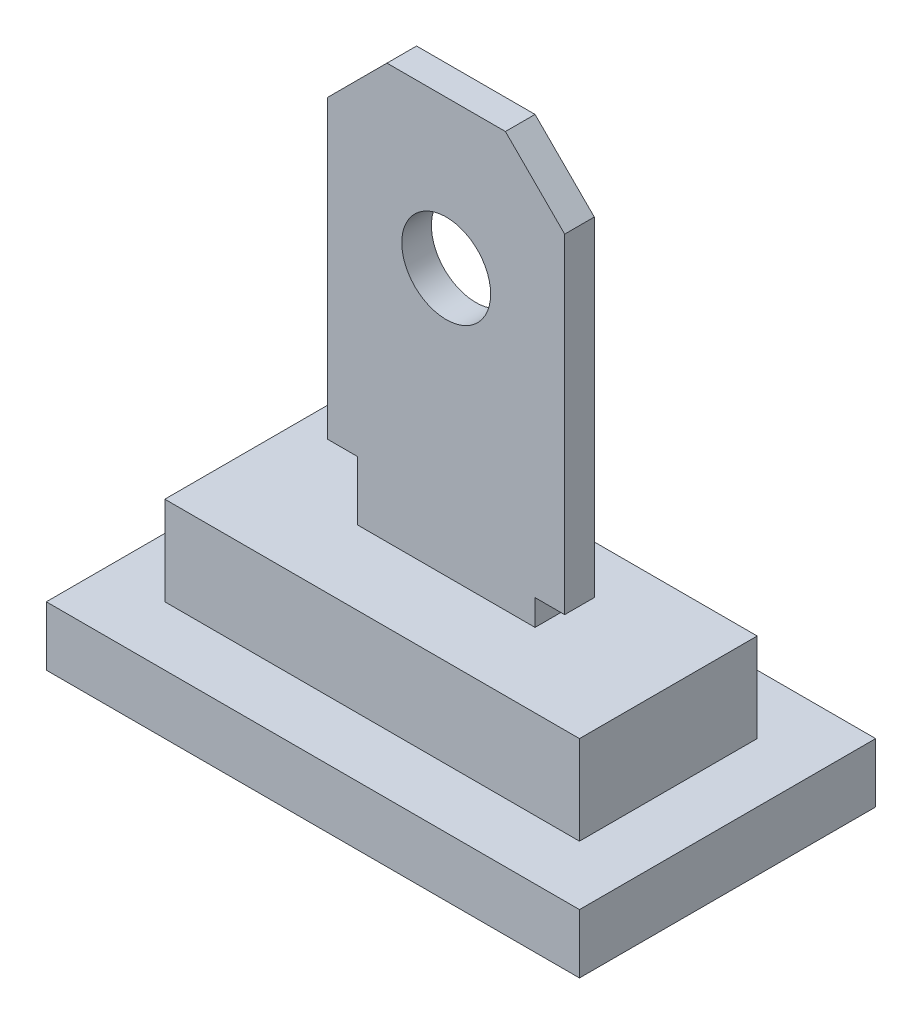
SolidWorks part; units mm, degrees
ref_plane "Front Plane" through (0, 0, 0) normal (0, 0, 1) x (1, 0, 0)
ref_plane "Top Plane" through (0, 0, 0) normal (0, 1, 0) x (1, 0, 0)
ref_plane "Right Plane" through (0, 0, 0) normal (1, 0, 0) x (0, 0, -1)
sketch "Sketch1" plane through (0, 0, 0) normal (0, 1, 0) x (1, 0, 0)
  line L1 (-3.5, 1.5) -> (3.5, 1.5)
  line L2 (-3.5, 1.5) -> (-3.5, -1.5)
  line L3 (-3.5, -1.5) -> (3.5, -1.5)
  line L4 (3.5, 1.5) -> (3.5, -1.5)
  line L5 (-3.5, 1.5) -> (3.5, -1.5) construction
  line L6 (-3.5, -1.5) -> (3.5, 1.5) construction
  point P0 (0, 0)
  dimension "D1" = 7
  dimension "D2" = 3
extrude "Boss-Extrude1" add sketch "Sketch1" along normal blind 1.5
sketch "Sketch2" plane through (0, 0, 0) normal (0, -1, 0) x (1, 0, 0)
  line L0 (-3.5, 1.5) -> (3.5, 1.5) construction
  line L1 (-4.5, 2.5) -> (4.5, 2.5)
  line L2 (-4.5, 2.5) -> (-4.5, -2.5)
  line L3 (-4.5, -2.5) -> (4.5, -2.5)
  line L4 (4.5, 2.5) -> (4.5, -2.5)
  line L5 (-4.5, 2.5) -> (4.5, -2.5) construction
  line L6 (-4.5, -2.5) -> (4.5, 2.5) construction
  line L7 (-3.5, -1.5) -> (-3.5, 1.5) construction
  point P0 (0, 0)
  dimension "D1" = 1
  dimension "D2" = 1
extrude "Boss-Extrude2" add sketch "Sketch2" along normal blind 1
sketch "Sketch3" plane through (0, 0, 0) normal (0, 0, 1) x (1, 0, 0)
  line L0 (0, 8.5) -> (0, 0) construction
  line L1 (-1.5, 1.5) -> (-1.5, 2.5)
  line L2 (-3.5, 1.5) -> (3.5, 1.5) construction
  line L3 (-1.5, 2.5) -> (-2, 2.5)
  line L4 (-2, 2.5) -> (-2, 7.5)
  line L5 (-2, 7.5) -> (-1, 8.5)
  line L6 (-1, 8.5) -> (1, 8.5)
  line L7 (1, 8.5) -> (2, 7.5)
  line L8 (2, 7.5) -> (2, 1.9364)
  line L9 (2, 1.9364) -> (1.5, 1.9364)
  line L10 (1.5, 1.9364) -> (1.5, 1.5)
  line L11 (1.5, 1.5) -> (-1.5, 1.5)
  circle A0 centre (0, 6) radius 0.75
  dimension "D7" = 1.5
  dimension "D1" = 135
  dimension "D2" = 2
  dimension "D3" = 4
  dimension "D4" = 3
  dimension "D5" = 7
  dimension "D6" = 1
  dimension "D8" = 2.5
extrude "Boss-Extrude3" add sketch "Sketch3" along normal mid plane 0.5
equation "\"D2@Sketch1\" = \"D1@Sketch1\" / 2.5"
